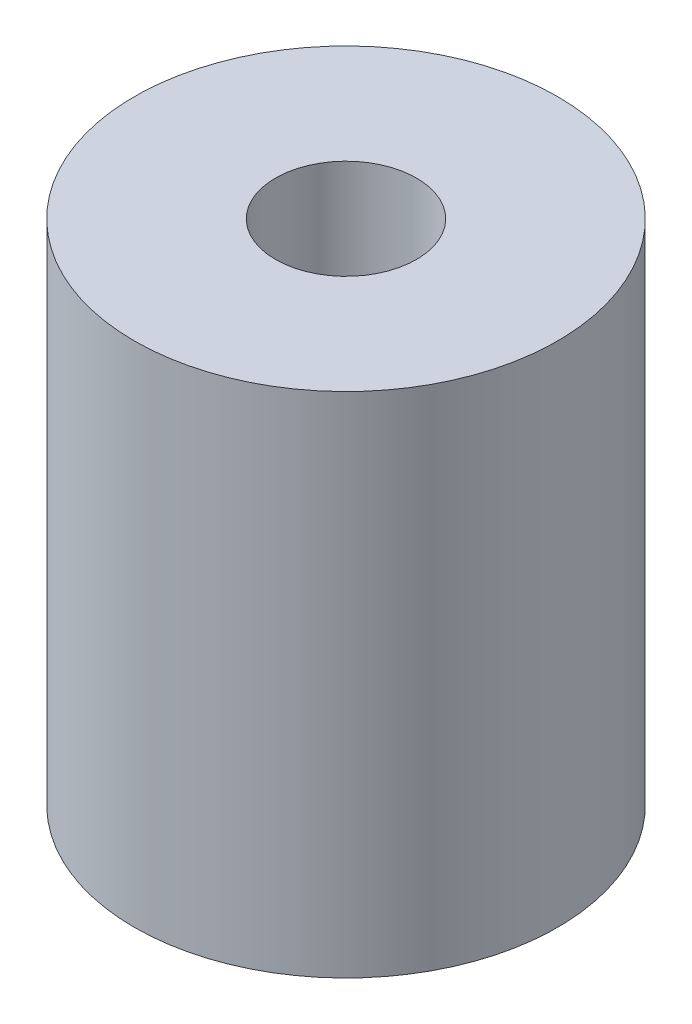
SolidWorks part; units mm, degrees
ref_plane "Face" through (0, 0, 0) normal (0, 0, 1) x (1, 0, 0)
ref_plane "Dessus" through (0, 0, 0) normal (0, 1, 0) x (1, 0, 0)
ref_plane "Droite" through (0, 0, 0) normal (1, 0, 0) x (0, 0, -1)
sketch "Esquisse1" plane through (0, 0, 0) normal (0, 1, 0) x (1, 0, 0)
  circle A0 centre (0, 0) radius 15
  circle A1 centre (0, 0) radius 5
  dimension "D1" = 30
  dimension "D2" = 10
extrude "Extrusion1" add sketch "Esquisse1" along normal blind 36
